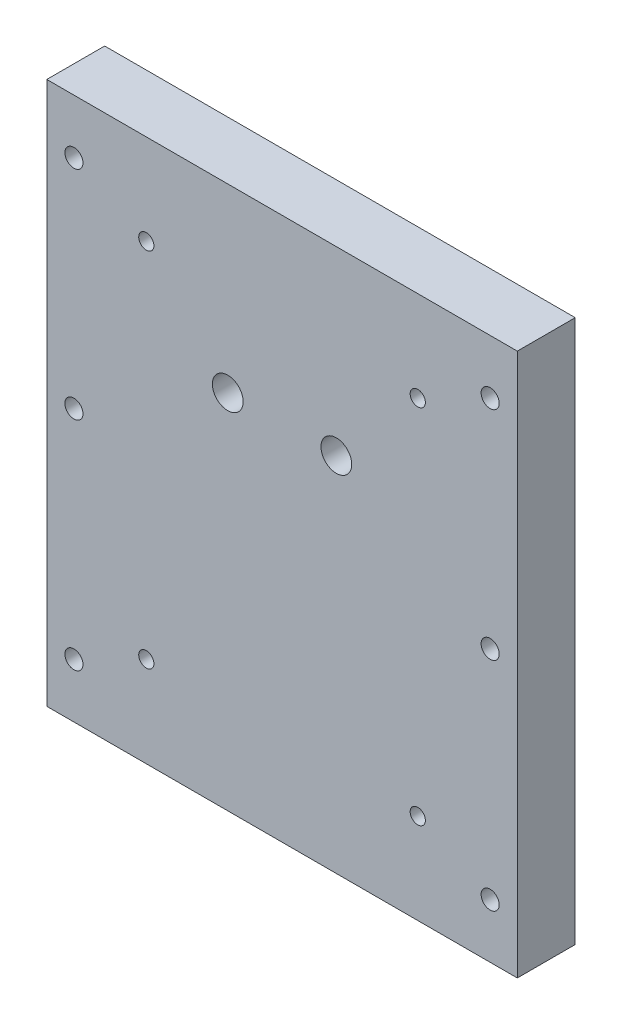
SolidWorks part; units mm, degrees
material "1023 Листовая углеродистая сталь (SS)"
ref_plane "Front" through (0, 0, 0) normal (0, 0, 1) x (1, 0, 0)
ref_plane "Top" through (0, 0, 0) normal (0, 1, 0) x (1, 0, 0)
ref_plane "Right" through (0, 0, 0) normal (1, 0, 0) x (0, 0, -1)
sketch "Sketch1" plane through (0, 0, 0) normal (0, 0, 1) x (1, 0, 0)
  line L1 (-65, 75) -> (65, 75)
  line L2 (-65, 75) -> (-65, -75)
  line L3 (-65, -75) -> (65, -75)
  line L4 (65, 75) -> (65, -75)
  line L5 (-65, 75) -> (65, -75) construction
  line L6 (-65, -75) -> (65, 75) construction
  point P0 (0, 0)
  dimension "D1" = 150
  dimension "D2" = 130
extrude "Extrude1" add sketch "Sketch1" along normal blind 16
hole_wizard "M6 Tapped Hole1" positions "Sketch3" profile "Sketch4" tap size "M6" standard "DIN" end condition through all
sketch "Sketch3" plane through (0, 0, 16) normal (0, 0, 1) x (1, 0, 0)
  line L0 (-65, 75) -> (-65, -75) construction
  line L1 (0, 0) -> (0, 15.036) construction
  point P0 (-57.5, 60)
  point P2 (-57.5, 0)
  point P4 (-57.5, -60)
  point P16 (57.5, -60)
  point P17 (57.5, 0)
  point P18 (57.5, 60)
  dimension "D1" = 7.5
  dimension "D2" = 60
  dimension "D3" = 60
sketch "Sketch4" plane through (-57.5, 60, 16) normal (1, 0, 0) x (0, -1, 0)
  line L0 (0, 0) -> (0, 16)
  line L1 (0, 16) -> (2.5, 16)
  line L2 (2.5, 16) -> (2.5, 0)
  line L5 (2.5, 0) -> (0, 0)
  line L11 (0, -6.35) -> (0, 107.95) construction
  dimension "Диаметр проходного сверла" = 5
  dimension "Глубина проходного сверла" = 16
cosmetic thread "Cosmetic Thread1"
cosmetic thread "Cosmetic Thread2"
cosmetic thread "Cosmetic Thread3"
cosmetic thread "Cosmetic Thread4"
cosmetic thread "Cosmetic Thread5"
cosmetic thread "Cosmetic Thread6"
hole_wizard "M5 Tapped Hole1" positions "Sketch5" profile "Sketch6" tap size "M5" standard "DIN" end condition up to next
sketch "Sketch5" plane through (0, 0, 16) normal (0, 0, 1) x (1, 0, 0)
  point P0 (-37.5, 50)
  point P3 (37.5, 50)
  point P10 (37.5, -50)
  point P13 (-37.5, -50)
sketch "Sketch6" plane through (-37.5, 50, 16) normal (1, 0, 0) x (0, -1, 0)
  line L0 (0, 0) -> (0, 16)
  line L1 (0, 16) -> (2.1, 16)
  line L2 (2.1, 16) -> (2.1, 0)
  line L5 (2.1, 0) -> (0, 0)
  line L11 (0, -6.35) -> (0, 107.95) construction
  dimension "Диаметр проходного сверла" = 4.2
  dimension "Глубина проходного сверла" = 16
cosmetic thread "Cosmetic Thread7"
cosmetic thread "Cosmetic Thread8"
cosmetic thread "Cosmetic Thread9"
cosmetic thread "Cosmetic Thread10"
hole_wizard "M10 Tapped Hole1" positions "Sketch7" profile "Sketch8" tap size "M10" standard "DIN"
sketch "Sketch7" plane through (0, 0, 0) normal (0, 0, -1) x (-1, 0, 0)
  point P0 (-15, 25)
sketch "Sketch8" plane through (15, 25, 0) normal (1, 0, 0) x (0, 1, 0)
  line L0 (0, 0) -> (0, 30.0537)
  line L1 (0, 30.0537) -> (4.25, 27.5)
  line L2 (4.25, 27.5) -> (4.25, 0)
  line L5 (4.25, 0) -> (0, 0)
  line L10 (0, 30.0537) -> (-4.25, 27.5) construction
  line L11 (0, -6.35) -> (0, 107.95) construction
  dimension "Диаметр сверла" = 8.5
  dimension "Глубина сверла" = 27.5
  dimension "Угол заточки сверла" = 118
cosmetic thread "Cosmetic Thread11"
hole_wizard "M10 Tapped Hole2" positions "Sketch9" profile "Sketch10" tap size "M10" standard "DIN"
sketch "Sketch9" plane through (0, 0, 0) normal (0, 0, -1) x (-1, 0, 0)
  point P0 (15, 25)
sketch "Sketch10" plane through (-15, 25, 0) normal (1, 0, 0) x (0, 1, 0)
  line L0 (0, 0) -> (0, 30.0537)
  line L1 (0, 30.0537) -> (4.25, 27.5)
  line L2 (4.25, 27.5) -> (4.25, 0)
  line L5 (4.25, 0) -> (0, 0)
  line L10 (0, 30.0537) -> (-4.25, 27.5) construction
  line L11 (0, -6.35) -> (0, 107.95) construction
  dimension "Диаметр сверла" = 8.5
  dimension "Глубина сверла" = 27.5
  dimension "Угол заточки сверла" = 118
cosmetic thread "Cosmetic Thread12"
